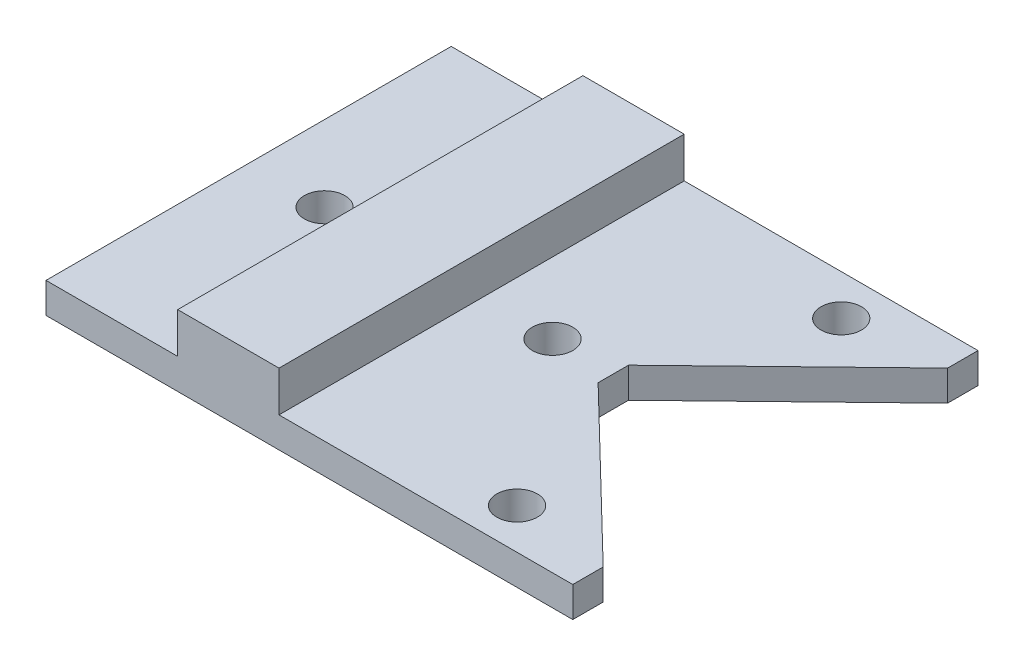
SolidWorks part; units mm, degrees
ref_plane "Front Plane" through (0, 0, 0) normal (0, 0, 1) x (1, 0, 0)
ref_plane "Top Plane" through (0, 0, 0) normal (0, 1, 0) x (1, 0, 0)
ref_plane "Right Plane" through (0, 0, 0) normal (1, 0, 0) x (0, 0, -1)
sketch "BaseSketch" plane through (0, 0, 0) normal (0, 1, 0) x (1, 0, 0)
  line L0 (26, -20) -> (26, -17)
  line L5 (26, -20) -> (-26, -20)
  line L10 (26, 20) -> (-26, 20)
  line L11 (-26, -20) -> (-26, 20)
  line L12 (26, -20) -> (-26, 20) construction
  line L13 (26, 20) -> (-26, -20) construction
  line L14 (26, 20) -> (26, 17)
  line L15 (-26, 0) -> (10, 0) construction
  line L16 (10, -1.5) -> (10, 1.5)
  line L17 (26, 17) -> (10, 1.5)
  line L18 (10, -1.5) -> (26, -17)
  point P0 (0, 0)
  point P13 (10, 0)
  dimension "D1" = 52
  dimension "D2" = 40
  dimension "D3" = 3
  dimension "D4" = 36
  dimension "D5" = 3
extrude "Base" add sketch "BaseSketch" along normal blind 3
sketch "BuldgeSketch" plane through (0, 3, 0) normal (0, 1, 0) x (1, 0, 0)
  line L0 (-26, -20) -> (26, -20) construction
  line L1 (-3, -20) -> (-13, -20)
  line L2 (-3, -20) -> (-3, 20)
  line L3 (-3, 20) -> (-13, 20)
  line L4 (-13, -20) -> (-13, 20)
  line L5 (26, 20) -> (-26, 20) construction
  line L6 (-26, 20) -> (-26, -20) construction
  dimension "D1" = 13
  dimension "D2" = 10
extrude "Buldge" add sketch "BuldgeSketch" along normal blind 4
sketch "HolesSketch" plane through (0, 0, 0) normal (0, -1, 0) x (1, 0, 0)
  line L0 (-26, -16) -> (16.5, -16) construction
  line L1 (-26, -20) -> (-26, 20) construction
  line L2 (-26, 16) -> (16.5, 16) construction
  line L3 (4, 0) -> (-18.5, 0) construction
  line L4 (-18.5, 0) -> (-26, 0) construction
  line L5 (-26, -20) -> (-26, 20) construction
  line L6 (26, -20) -> (-26, -20) construction
  line L7 (-26, 20) -> (26, 20) construction
  circle A1 centre (4, 0) radius 2
  circle A2 centre (16.5, -16) radius 2
  circle A4 centre (16.5, 16) radius 2
  circle A5 centre (-18.5, 0) radius 2
  dimension "D6" = 4
  dimension "D1" = 4
  dimension "D2" = 4
  dimension "D3" = 7.5
  dimension "D4" = 42.5
  dimension "D5" = 22.5
extrude "Holes" cut sketch "HolesSketch" against normal through all both and the other way through all
